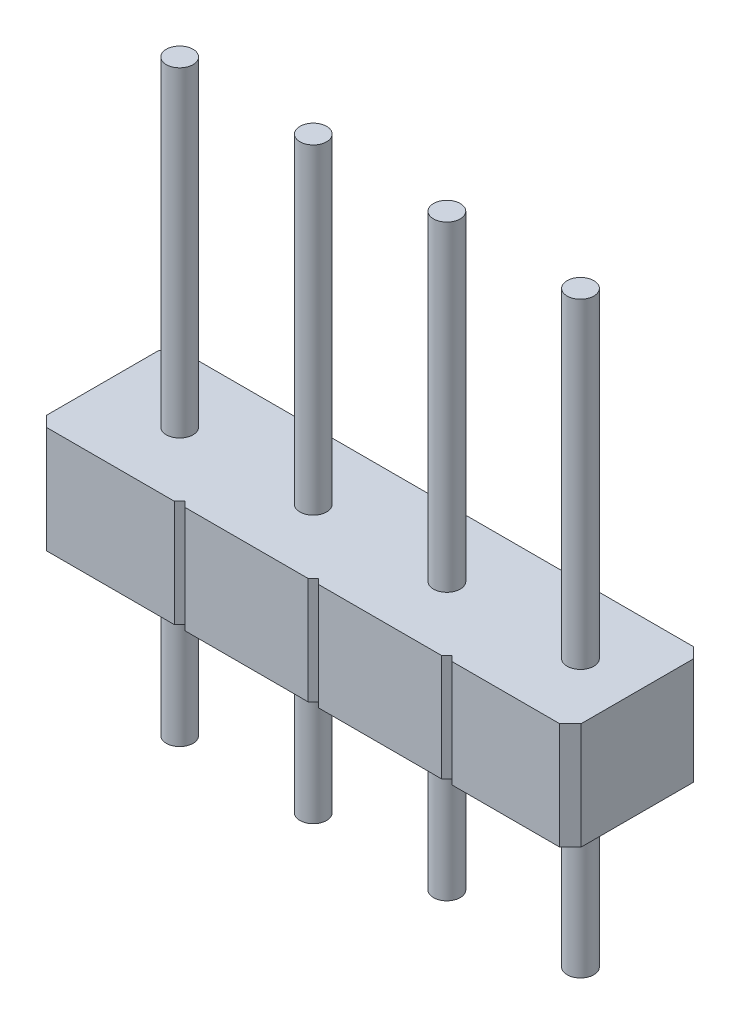
SolidWorks part; units mm, degrees
ref_plane "Ön Düzlem" through (0, 0, 0) normal (0, 0, 1) x (1, 0, 0)
ref_plane "Üst Düzlem" through (0, 0, 0) normal (0, 1, 0) x (1, 0, 0)
ref_plane "Sağ Düzlem" through (0, 0, 0) normal (1, 0, 0) x (0, 0, -1)
sketch "Çizim1" plane through (0, 0, 0) normal (0, 1, 0) x (1, 0, 0)
  line L1 (-4.8, 1.25) -> (-2.4121, 1.25)
  line L2 (-5, 1.05) -> (-5, -1.05)
  line L3 (-4.8, -1.25) -> (-2.4114, -1.25)
  line L4 (5, 1.05) -> (5, -1.05)
  line L5 (-5, 1.25) -> (5, -1.25) construction
  line L6 (-5, -1.25) -> (5, 1.25) construction
  line L7 (-4.8114, 0) -> (5.1886, 0) construction
  line L8 (-5, 1.05) -> (-4.8, 1.25)
  line L9 (-5, -1.05) -> (-4.8, -1.25)
  line L10 (4.8, 1.25) -> (5, 1.05)
  line L11 (4.8, -1.25) -> (5, -1.05)
  line L15 (-2.4121, 1.25) -> (-2.3114, 1.1223)
  line L16 (-2.3114, 1.1223) -> (-2.2107, 1.25)
  line L17 (0.0886, 1.25) -> (0.1886, 1.15)
  line L18 (0.1886, 1.15) -> (0.2886, 1.25)
  line L19 (2.5886, 1.25) -> (2.6886, 1.15)
  line L20 (2.6886, 1.15) -> (2.7886, 1.25)
  line L21 (2.5886, -1.25) -> (2.6886, -1.15)
  line L22 (2.6886, -1.15) -> (2.7886, -1.25)
  line L23 (0.0886, -1.25) -> (0.1886, -1.15)
  line L24 (0.1886, -1.15) -> (0.2886, -1.25)
  line L25 (-2.4114, -1.25) -> (-2.3114, -1.15)
  line L26 (-2.3114, -1.15) -> (-2.2114, -1.25)
  line L27 (-2.2107, 1.25) -> (0.0886, 1.25)
  line L28 (0.2886, 1.25) -> (2.5886, 1.25)
  line L29 (2.7886, 1.25) -> (4.8, 1.25)
  line L30 (2.7886, -1.25) -> (4.8, -1.25)
  line L31 (0.2886, -1.25) -> (2.5886, -1.25)
  line L32 (-2.2114, -1.25) -> (0.0886, -1.25)
  circle A0 centre (-3.5614, 0) radius 0.25
  circle A1 centre (-1.0614, 0) radius 0.25
  circle A2 centre (1.4386, 0) radius 0.25
  circle A3 centre (3.9386, 0) radius 0.25
  point P0 (0, 0)
  point P6 (2.5886, 1.25)
  point P7 (-2.3114, -1.15)
  point P26 (0.0886, 1.25)
  point P28 (0.0886, -1.25)
  point P29 (0.1886, -1.15)
  point P32 (0.2886, 1.25)
  point P34 (0.1886, 1.15)
  point P35 (2.7886, 1.25)
  point P37 (2.6886, 1.15)
  point P42 (0.2886, -1.25)
  point P44 (-2.2114, -1.25)
  point P46 (-2.4114, -1.25)
  dimension "D3" = 0.5
  dimension "D6" = 2.5
  dimension "D7" = 2.5
  dimension "D1" = 10
  dimension "D2" = 2.5
extrude "Yükseklik-Ekstrüzyon1" add sketch "Çizim1" along normal blind 2
sketch "Çizim2" plane through (0, 2, 0) normal (0, 1, 0) x (1, 0, 0)
  circle A0 centre (-3.5614, 0) radius 0.25
  circle A1 centre (-1.0614, 0) radius 0.25
  circle A2 centre (1.4386, 0) radius 0.25
  circle A3 centre (3.9386, 0) radius 0.25
extrude "Yükseklik-Ekstrüzyon2" add sketch "Çizim2" along normal blind 6 and the other way blind 5
